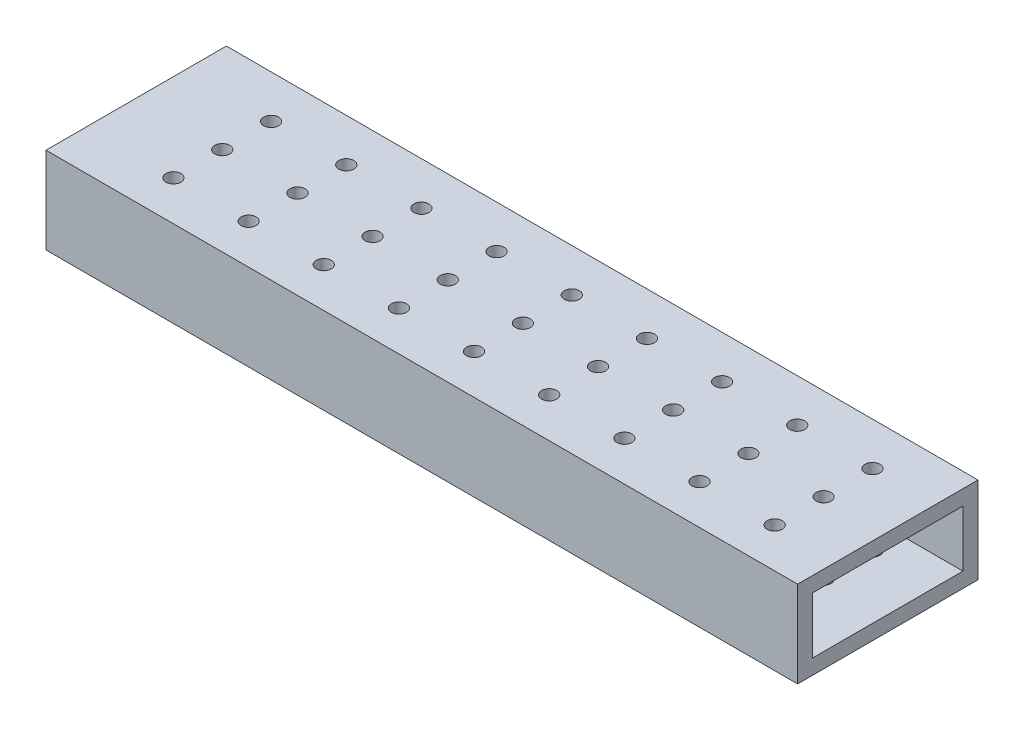
SolidWorks part; units mm, degrees
ref_plane "Front Plane" through (0, 0, 0) normal (0, 0, 1) x (1, 0, 0)
ref_plane "Top Plane" through (0, 0, 0) normal (0, 1, 0) x (1, 0, 0)
ref_plane "Right Plane" through (0, 0, 0) normal (1, 0, 0) x (0, 0, -1)
sketch "Sketch1" plane through (0, 0, 0) normal (1, 0, 0) x (0, 0, -1)
  line L1 (-20, 7.5) -> (20, 7.5)
  line L2 (-20, 7.5) -> (-20, -7.5)
  line L3 (-20, -7.5) -> (20, -7.5)
  line L4 (20, 7.5) -> (20, -7.5)
  line L5 (-20, 7.5) -> (20, -7.5) construction
  line L6 (-20, -7.5) -> (20, 7.5) construction
  point P0 (0, 0)
  dimension "D1" = 40
  dimension "D2" = 15
extrude "Extrude-Thin1" add sketch "Sketch1" along normal mid plane 200 thin thin type one direction wall 4
sketch "Sketch2" plane through (0, 11.5, 0) normal (0, 1, 0) x (1, 0, 0)
  circle A0 centre (-76.6785, 12.5831) radius 2
  circle A1 centre (-56.6785, 12.5831) radius 2
  circle A2 centre (-36.6785, 12.5831) radius 2
  circle A3 centre (-16.6785, 12.5831) radius 2
  circle A4 centre (3.3215, 12.5831) radius 2
  circle A5 centre (23.3215, 12.5831) radius 2
  circle A6 centre (43.3215, 12.5831) radius 2
  circle A7 centre (63.3215, 12.5831) radius 2
  circle A8 centre (83.3215, 12.5831) radius 2
  circle A9 centre (-56.6785, -0.4169) radius 2
  circle A10 centre (-36.6785, -0.4169) radius 2
  circle A11 centre (-16.6785, -0.4169) radius 2
  circle A12 centre (3.3215, -0.4169) radius 2
  circle A13 centre (23.3215, -0.4169) radius 2
  circle A14 centre (43.3215, -0.4169) radius 2
  circle A15 centre (63.3215, -0.4169) radius 2
  circle A16 centre (83.3215, -0.4169) radius 2
  circle A17 centre (-56.6785, -13.4169) radius 2
  circle A18 centre (-36.6785, -13.4169) radius 2
  circle A19 centre (-16.6785, -13.4169) radius 2
  circle A20 centre (3.3215, -13.4169) radius 2
  circle A21 centre (23.3215, -13.4169) radius 2
  circle A22 centre (43.3215, -13.4169) radius 2
  circle A23 centre (63.3215, -13.4169) radius 2
  circle A24 centre (83.3215, -13.4169) radius 2
  circle A25 centre (-76.6785, -0.4169) radius 2
  circle A26 centre (-76.6785, -13.4169) radius 2
  dimension "D1" = 9
  dimension "D2" = 3
extrude "Cut-Extrude1" cut sketch "Sketch2" against normal through all
